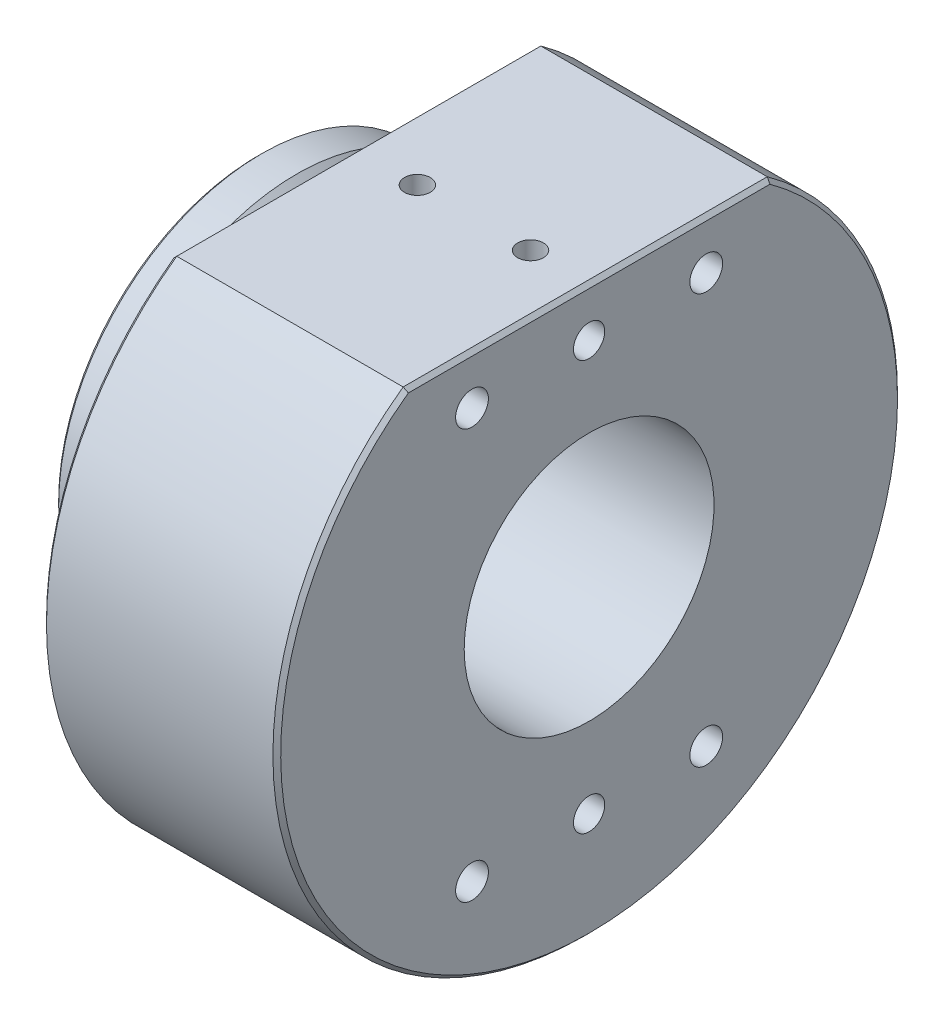
SolidWorks part; units mm, degrees
ref_plane "Front Plane" through (0, 0, 0) normal (0, 0, 1) x (1, 0, 0)
ref_plane "Top Plane" through (0, 0, 0) normal (0, 1, 0) x (1, 0, 0)
ref_plane "Right Plane" through (0, 0, 0) normal (1, 0, 0) x (0, 0, -1)
sketch "Sketch1" plane through (0, 0, 0) normal (0, 0, 1) x (1, 0, 0)
  line L0 (-39.7386, 0) -> (59.3987, 0) construction
  line L1 (-27.5819, 26) -> (-22.5819, 26)
  line L2 (-22.5819, 26) -> (-19.3615, 22.7796)
  line L3 (-19.3615, 22.7796) -> (-16.1411, 26)
  line L4 (-16.1411, 26) -> (-15.1411, 26)
  line L5 (-15.1411, 26) -> (-15.1411, 40)
  line L6 (-15.1411, 40) -> (14.8589, 40)
  line L7 (14.8589, 40) -> (14.8589, 16)
  line L8 (14.8589, 16) -> (-27.5819, 16)
  line L9 (-27.5819, 16) -> (-27.5819, 26)
  point P12 (-15.6411, 26)
  dimension "D1" = 80
  dimension "D2" = 52
  dimension "D3" = 5
  dimension "D4" = 1
  dimension "D5" = 90
  dimension "D6" = 32
  dimension "D7" = 30
revolve "Revolve1" add sketch "Sketch1" angle 360 about L0
chamfer "Chamfer1" distance 0.5 angle 45 3 edges at (14.8589, 0, 40) (-15.1411, 0, 40) (-27.5819, 0, 26)
ref_plane "Plane1" through (0, 40, 0) normal (0, 1, 0) x (1, 0, 0)
sketch "Sketch3" plane through (0, 40, 0) normal (0, 1, 0) x (1, 0, 0)
  line L1 (-15.5273, 41.2305) -> (15.3875, 41.2305)
  line L2 (-15.5273, 41.2305) -> (-15.5273, -40.7806)
  line L3 (-15.5273, -40.7806) -> (15.3875, -40.7806)
  line L4 (15.3875, 41.2305) -> (15.3875, -40.7806)
  line L5 (-15.5273, 41.2305) -> (15.3875, -40.7806) construction
  line L6 (-15.5273, -40.7806) -> (15.3875, 41.2305) construction
  point P4 (-0.0699, 0.225)
extrude "Cut-Extrude2" cut sketch "Sketch3" against normal blind 7.5
chamfer "Chamfer2" distance 0.5 angle 45 2 edges at (14.8589, 32.5, 0) (-15.1411, 32.5, 0)
sketch "Sketch4" plane through (-15.1411, 0, 0) normal (-1, 0, 0) x (0, 0, 1)
  line L0 (0, 0) -> (0, 30.8798) construction
  circle A0 centre (0, 0) radius 29 construction
  dimension "D1" = 58
hole_wizard "3/16 (0.1875) Dowel Hole1" positions "Sketch5" profile "Sketch6" hole size "3/16" standard "ANSI Inch"
sketch "Sketch5" plane through (-15.1411, 0, 0) normal (-1, 0, 0) x (0, 0, 1)
  line L0 (-23.3184, 32.5) -> (23.3184, 32.5) construction
  point P0 (0, 29)
  point P1 (0, 0)
  dimension "D1" = 3.5
sketch "Sketch6" plane through (-15.1411, 29, 0) normal (0, 1, 0) x (0, 0, 1)
  line L0 (0, 0) -> (0, 6.9308)
  line L1 (0, 6.9308) -> (2.3812, 5.5)
  line L2 (2.3812, 5.5) -> (2.3812, 0)
  line L5 (2.3812, 0) -> (0, 0)
  line L10 (0, 6.9308) -> (-2.3813, 5.5) construction
  line L11 (0, -6.35) -> (0, 107.95) construction
  dimension "Hole Dia." = 4.7625
  dimension "Hole Depth" = 5.5
  dimension "Drill Angle" = 118
hole_wizard "M5x0.8 Tapped Hole1" positions "Sketch7" profile "Sketch8" tap size "M5x0.8" standard "ANSI Metric"
sketch "Sketch7" plane through (14.8589, 0, 0) normal (1, 0, 0) x (0, 0, -1)
  point P0 (-15, 26.25)
  point P3 (15, 26.25)
  point P6 (-15, -26.25)
  point P9 (15, -26.25)
  point P12 (0, 0)
  point P13 (0, 0)
  point P14 (0, 0)
  point P15 (0, 0)
  point P16 (0, 0)
  point P17 (0, 0)
  point P18 (0, 0)
  point P19 (0, 0)
  point P21 (0, 0)
  dimension "D1" = 30
  dimension "D2" = 52.5
  dimension "D3" = 15
  dimension "D4" = 26.25
sketch "Sketch8" plane through (14.8589, 26.25, 15) normal (0, 1, 0) x (0, 0, -1)
  line L0 (0, 0) -> (0, 13.6618)
  line L1 (0, 13.6618) -> (2.1, 12.4)
  line L2 (2.1, 12.4) -> (2.1, 0)
  line L5 (2.1, 0) -> (0, 0)
  line L10 (0, 13.6618) -> (-2.1, 12.4) construction
  line L11 (0, -6.35) -> (0, 107.95) construction
  dimension "Tap Drill Dia." = 4.2
  dimension "Tap Drill Depth" = 12.4
  dimension "Drill Angle" = 118
cosmetic thread "Hole Thread1" parameters "D1"=10, "D2"=5
cosmetic thread "Hole Thread2" parameters "D1"=10, "D2"=5
cosmetic thread "Hole Thread3" parameters "D1"=10, "D2"=5
cosmetic thread "Hole Thread4" parameters "D1"=10, "D2"=5
hole_wizard "Ø4.0mm Dowel Hole1" positions "Sketch10" profile "Sketch11" hole size "Ø4.0" standard "ANSI Metric"
sketch "Sketch10" plane through (14.8589, 0, 0) normal (1, 0, 0) x (0, 0, -1)
  point P0 (0, 26.25)
  point P6 (0, -26.25)
  point P12 (0, 0)
  point P13 (0, 0)
  point P15 (0, 0)
  dimension "D1" = 52.5
  dimension "D2" = 26.25
sketch "Sketch11" plane through (14.8589, 26.25, 0) normal (0, 1, 0) x (0, 0, -1)
  line L0 (0, 0) -> (0, 6.4017)
  line L1 (0, 6.4017) -> (2, 5.2)
  line L2 (2, 5.2) -> (2, 0)
  line L5 (2, 0) -> (0, 0)
  line L10 (0, 6.4017) -> (-2, 5.2) construction
  line L11 (0, -6.35) -> (0, 107.95) construction
  dimension "Hole Dia." = 4
  dimension "Hole Depth" = 5.2
  dimension "Drill Angle" = 118
hole_wizard "M4x0.7 Tapped Hole1" positions "Sketch12" profile "Sketch13" tap size "M4x0.7" standard "ANSI Metric"
sketch "Sketch12" plane through (0, 32.5, 0) normal (0, 1, 0) x (1, 0, 0)
  line L0 (-15.1411, 26) -> (-15.1411, -26) construction
  line L1 (14.8589, 23.1571) -> (14.8589, -23.1571) construction
  point P0 (-7.1411, 0)
  point P2 (7.3589, 0)
  point P9 (0, 0)
  dimension "D1" = 8
  dimension "D2" = 7.5
sketch "Sketch13" plane through (-7.1411, 32.5, 0) normal (1, 0, 0) x (0, 0, 1)
  line L0 (0, 0) -> (0, 16.5)
  line L1 (0, 16.5) -> (1.65, 16.5)
  line L2 (1.65, 16.5) -> (1.65, 0)
  line L5 (1.65, 0) -> (0, 0)
  line L11 (0, -6.35) -> (0, 107.95) construction
  dimension "Thru Tap Drill Dia." = 3.3
  dimension "Thru Tap Drill Depth" = 16.5
cosmetic thread "Hole Thread5" parameters "D2"=4
cosmetic thread "Hole Thread6" parameters "D2"=4
